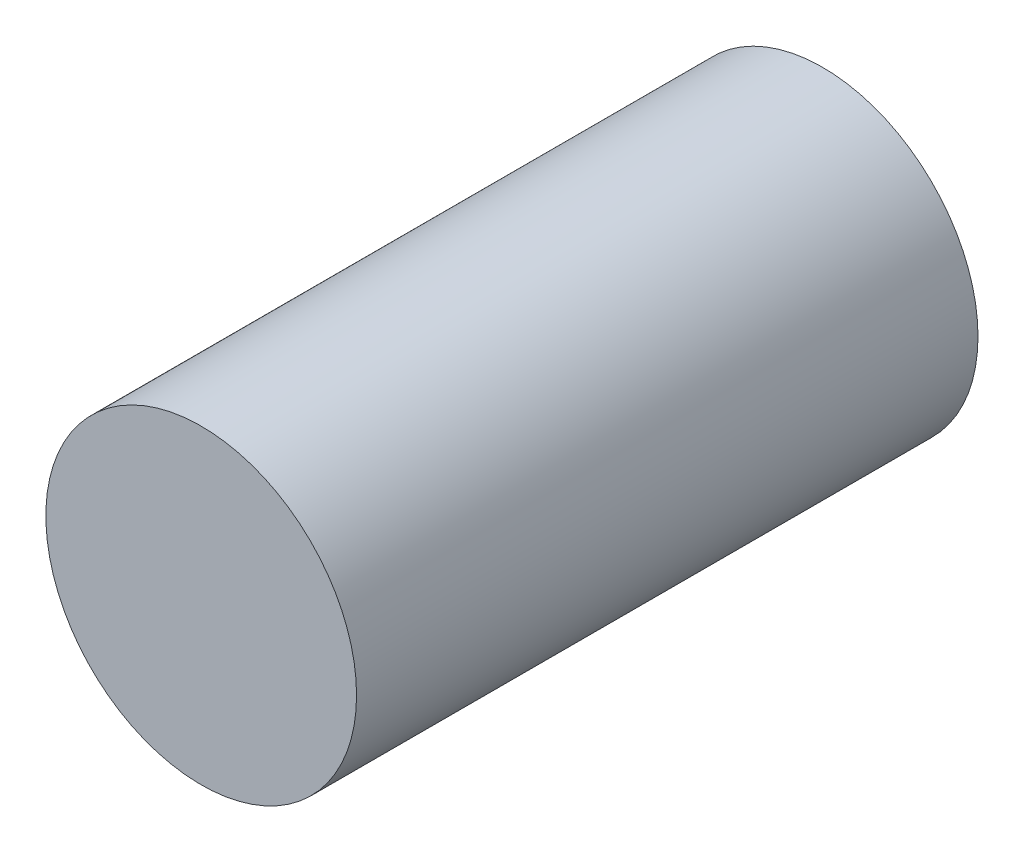
SolidWorks part; units mm, degrees
ref_plane "前视基准面" through (0, 0, 0) normal (0, 0, 1) x (1, 0, 0)
ref_plane "上视基准面" through (0, 0, 0) normal (0, 1, 0) x (1, 0, 0)
ref_plane "右视基准面" through (0, 0, 0) normal (1, 0, 0) x (0, 0, -1)
sketch "草图1" plane through (0, 0, 0) normal (0, 0, 1) x (1, 0, 0)
  circle A0 centre (0, 0) radius 1
  dimension "D1" = 2
extrude "凸台-拉伸1" add sketch "草图1" along normal blind 4
